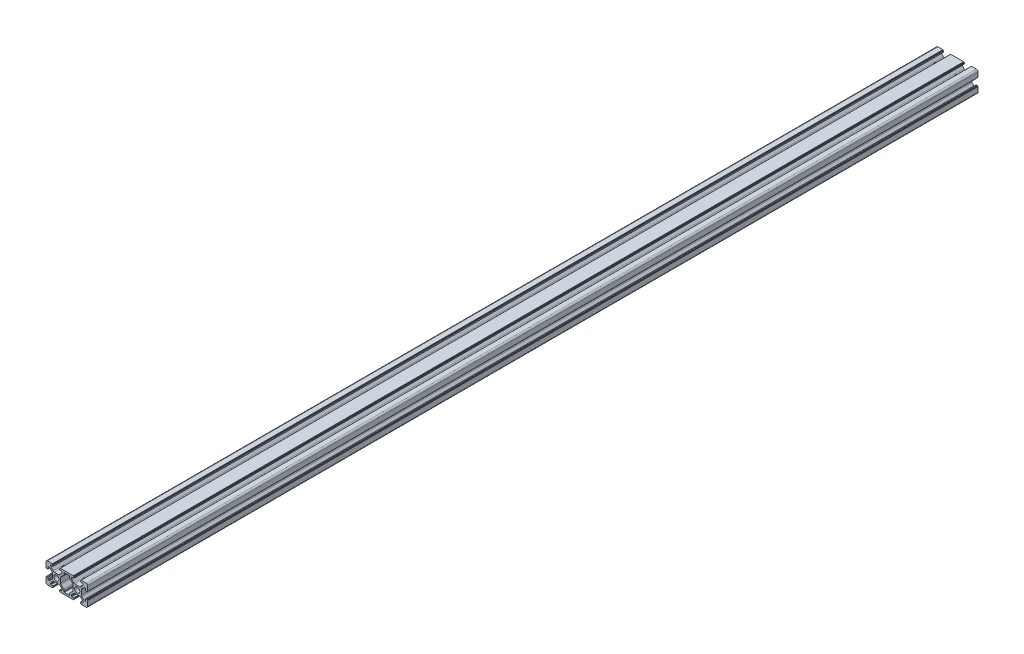
SolidWorks part; units mm, degrees
material "6063-O"
ref_plane "Front Plane" through (0, 0, 0) normal (0, 0, 1) x (1, 0, 0)
ref_plane "Top Plane" through (0, 0, 0) normal (0, 1, 0) x (1, 0, 0)
ref_plane "Right Plane" through (0, 0, 0) normal (1, 0, 0) x (0, 0, -1)
sketch "Sketch1" plane through (0, 0, 0) normal (0, 0, 1) x (1, 0, 0)
  line L0 (1.5, 0) -> (6.2, 0)
  line L1 (40, 1.5) -> (40, 6.2)
  line L2 (38.5, 20) -> (33.8, 20)
  line L3 (0, 18.5) -> (0, 13.8)
  line L4 (17.6, 1.8) -> (22.4, 1.8)
  line L5 (32.218, 13.9) -> (27.782, 13.9)
  line L6 (26.1, 12.218) -> (26.1, 7.782)
  line L7 (17.6, 18.2) -> (22.4, 18.2)
  line L8 (12.218, 13.9) -> (7.9864, 13.9)
  line L9 (6.1, 12.218) -> (6.1, 7.782)
  line L10 (7.782, 6.1) -> (12.218, 6.1)
  line L11 (13.9, 7.782) -> (13.9, 12.218)
  line L12 (27.782, 6.1) -> (32.218, 6.1)
  line L13 (33.9, 7.782) -> (33.9, 12.218)
  line L14 (26.7213, 14.3393) -> (24.9393, 16.1213)
  line L15 (33.2787, 14.3393) -> (35.0607, 16.1213)
  line L16 (34.3393, 13.2787) -> (36.1213, 15.0607)
  line L17 (25.6607, 6.7213) -> (23.1393, 4.2)
  line L18 (15.2, 1.8) -> (13.4, 1.8)
  line L19 (26.7213, 5.6607) -> (24.9393, 3.8787)
  line L20 (24.8, 1.8) -> (26.6, 1.8)
  line L21 (15.3, 18.2) -> (13.1, 18.2)
  line L22 (13.2787, 14.3393) -> (15.1607, 16.2213)
  line L23 (14.3393, 13.2787) -> (16.8607, 15.8)
  line L24 (5.6607, 6.7213) -> (3.8787, 4.9393)
  line L25 (6.7213, 5.6607) -> (4.9393, 3.8787)
  line L26 (6.897, 14.3689) -> (4.9106, 16.4674)
  line L27 (5.6607, 13.2787) -> (3.8787, 15.0607)
  line L28 (14.3393, 6.7213) -> (16.8607, 4.2)
  line L29 (13.2787, 5.6607) -> (15.0607, 3.8787)
  line L30 (24.8, 18.2) -> (26.6, 18.2)
  line L31 (25.6607, 13.2787) -> (23.1393, 15.8)
  line L32 (34.3393, 6.7213) -> (36.1213, 4.9393)
  line L33 (33.2787, 5.6607) -> (35.0607, 3.8787)
  line L34 (1.8, 15.2) -> (1.8, 13.4)
  line L35 (24.5, 2.1) -> (24.5, 2.818)
  line L36 (4.5, 2.1) -> (4.5, 2.818)
  line L37 (2.818, 4.5) -> (2.1, 4.5)
  line L38 (4.5, 17.9) -> (4.5, 17.4986)
  line L39 (2.818, 15.5) -> (2.1, 15.5)
  line L40 (15.6, 17.9) -> (15.6, 17.282)
  line L41 (15.5, 2.818) -> (15.5, 2.1)
  line L42 (38.2, 15.2) -> (38.2, 13.4)
  line L43 (35.5, 2.818) -> (35.5, 2.1)
  line L44 (37.182, 4.5) -> (37.9, 4.5)
  line L45 (35.5, 17.182) -> (35.5, 17.9)
  line L46 (37.182, 15.5) -> (37.9, 15.5)
  line L47 (17.3, 2.1) -> (17.3, 3.1393)
  line L48 (22.7, 2.1) -> (22.7, 3.1393)
  line L49 (17.3, 17.9) -> (17.3, 16.8607)
  line L50 (22.7, 17.9) -> (22.7, 16.8607)
  line L51 (24.5, 17.9) -> (24.5, 17.182)
  line L52 (6.9, 19.3) -> (6.9, 18.2)
  line L53 (13.1, 19.3) -> (13.1, 18.2)
  line L54 (6.9, 1.5) -> (6.9, 0.7)
  line L55 (13.1, 1.5) -> (13.1, 0.7)
  line L56 (13.8, 0) -> (26.2, 0)
  line L57 (6.6, 1.8) -> (4.8, 1.8)
  line L58 (6.9, 18.2) -> (4.8, 18.2)
  line L59 (6.2, 20) -> (1.5, 20)
  line L60 (39.3, 6.9) -> (38.5, 6.9)
  line L61 (39.3, 13.1) -> (38.5, 13.1)
  line L62 (1.5, 13.1) -> (0.7, 13.1)
  line L63 (1.5, 6.9) -> (0.7, 6.9)
  line L64 (0, 6.2) -> (0, 1.5)
  line L65 (1.8, 6.6) -> (1.8, 4.8)
  line L66 (38.2, 6.6) -> (38.2, 4.8)
  line L67 (40, 13.8) -> (40, 18.5)
  line L68 (33.1, 19.3) -> (33.1, 18.5)
  line L69 (26.9, 19.3) -> (26.9, 18.5)
  line L70 (26.9, 1.5) -> (26.9, 0.7)
  line L71 (33.1, 1.5) -> (33.1, 0.7)
  line L72 (33.8, 0) -> (38.5, 0)
  line L73 (33.4, 1.8) -> (35.2, 1.8)
  line L74 (26.2, 20) -> (13.8, 20)
  line L75 (33.4, 18.2) -> (35.2, 18.2)
  line L76 (6.7, 0.5) -> (6.6, 0.5)
  line L77 (6.4, 0.3) -> (6.4, 0.2)
  line L78 (13.3, 0.5) -> (13.4, 0.5)
  line L79 (13.6, 0.3) -> (13.6, 0.2)
  line L80 (26.7, 0.5) -> (26.6, 0.5)
  line L81 (26.4, 0.3) -> (26.4, 0.2)
  line L82 (33.3, 0.5) -> (33.4, 0.5)
  line L83 (33.6, 0.3) -> (33.6, 0.2)
  line L85 (6.4, 19.8) -> (6.4, 19.7)
  line L86 (6.6, 19.5) -> (6.7, 19.5)
  line L87 (13.6, 19.8) -> (13.6, 19.7)
  line L88 (13.4, 19.5) -> (13.3, 19.5)
  line L89 (26.4, 19.8) -> (26.4, 19.7)
  line L90 (26.6, 19.5) -> (26.7, 19.5)
  line L91 (33.6, 19.8) -> (33.6, 19.7)
  line L92 (33.4, 19.5) -> (33.3, 19.5)
  line L93 (0.5, 13.3) -> (0.5, 13.4)
  line L94 (0.3, 13.6) -> (0.2, 13.6)
  line L95 (0.5, 6.7) -> (0.5, 6.6)
  line L96 (0.3, 6.4) -> (0.2, 6.4)
  line L97 (39.5, 13.3) -> (39.5, 13.4)
  line L98 (39.7, 13.6) -> (39.8, 13.6)
  line L99 (39.5, 6.7) -> (39.5, 6.6)
  line L100 (39.7, 6.4) -> (39.8, 6.4)
  circle A0 centre (10, 10) radius 2.5
  circle A1 centre (30, 10) radius 2.5
  arc A2 (38.5, 0) -> (40, 1.5) centre (38.5, 1.5) ccw
  arc A3 (40, 18.5) -> (38.5, 20) centre (38.5, 18.5) ccw
  arc A4 (1.5, 0) -> (0, 1.5) centre (1.5, 1.5) cw
  arc A5 (1.5, 20) -> (0, 18.5) centre (1.5, 18.5) ccw
  arc A6 (26.7213, 5.6607) -> (27.782, 6.1) centre (27.782, 4.6) cw
  arc A7 (32.218, 6.1) -> (33.2787, 5.6607) centre (32.218, 4.6) cw
  arc A8 (33.9, 7.782) -> (34.3393, 6.7213) centre (35.4, 7.782) ccw
  arc A9 (33.2787, 14.3393) -> (32.218, 13.9) centre (32.218, 15.4) cw
  arc A10 (14.3393, 6.7213) -> (13.9, 7.782) centre (15.4, 7.782) cw
  arc A11 (14.3393, 13.2787) -> (13.9, 12.218) centre (15.4, 12.218) ccw
  arc A12 (25.6607, 6.7213) -> (26.1, 7.782) centre (24.6, 7.782) ccw
  arc A13 (26.1, 12.218) -> (25.6607, 13.2787) centre (24.6, 12.218) ccw
  arc A14 (27.782, 13.9) -> (26.7213, 14.3393) centre (27.782, 15.4) cw
  arc A15 (5.6607, 13.2787) -> (6.1, 12.218) centre (4.6, 12.218) cw
  arc A16 (5.6607, 6.7213) -> (6.1, 7.782) centre (4.6, 7.782) ccw
  arc A17 (13.2787, 5.6607) -> (12.218, 6.1) centre (12.218, 4.6) ccw
  arc A18 (6.7213, 5.6607) -> (7.782, 6.1) centre (7.782, 4.6) cw
  arc A19 (13.2787, 14.3393) -> (12.218, 13.9) centre (12.218, 15.4) cw
  arc A20 (6.897, 14.3689) -> (7.9864, 13.9) centre (7.9864, 15.4) ccw
  arc A21 (36.1213, 4.9393) -> (37.182, 4.5) centre (37.182, 6) ccw
  arc A22 (36.1213, 15.0607) -> (37.182, 15.5) centre (37.182, 14) cw
  arc A23 (35.0607, 16.1213) -> (35.5, 17.182) centre (34, 17.182) ccw
  arc A24 (24.5, 17.182) -> (24.9393, 16.1213) centre (26, 17.182) ccw
  arc A25 (22.7, 16.8607) -> (23.1393, 15.8) centre (24.2, 16.8607) ccw
  arc A26 (17.3, 16.8607) -> (16.8607, 15.8) centre (15.8, 16.8607) cw
  arc A27 (4.9106, 16.4674) -> (4.5, 17.4986) centre (6, 17.4986) cw
  arc A28 (15.6, 17.282) -> (15.1607, 16.2213) centre (14.1, 17.282) cw
  arc A29 (3.8787, 15.0607) -> (2.818, 15.5) centre (2.818, 14) ccw
  arc A30 (3.8787, 4.9393) -> (2.818, 4.5) centre (2.818, 6) cw
  arc A31 (4.9393, 3.8787) -> (4.5, 2.818) centre (6, 2.818) ccw
  arc A32 (35.0607, 3.8787) -> (35.5, 2.818) centre (34, 2.818) cw
  arc A33 (24.9393, 3.8787) -> (24.5, 2.818) centre (26, 2.818) ccw
  arc A34 (22.7, 3.1393) -> (23.1393, 4.2) centre (24.2, 3.1393) cw
  arc A35 (17.3, 3.1393) -> (16.8607, 4.2) centre (15.8, 3.1393) ccw
  arc A36 (15.5, 2.818) -> (15.0607, 3.8787) centre (14, 2.818) ccw
  arc A37 (1.8, 6.6) -> (1.5, 6.9) centre (1.5, 6.6) ccw
  arc A38 (1.8, 13.4) -> (1.5, 13.1) centre (1.5, 13.4) cw
  arc A39 (17.6, 18.2) -> (17.3, 17.9) centre (17.6, 17.9) ccw
  arc A40 (22.4, 1.8) -> (22.7, 2.1) centre (22.4, 2.1) ccw
  arc A41 (17.6, 1.8) -> (17.3, 2.1) centre (17.6, 2.1) cw
  arc A42 (15.2, 1.8) -> (15.5, 2.1) centre (15.2, 2.1) ccw
  arc A43 (6.6, 1.8) -> (6.9, 1.5) centre (6.6, 1.5) cw
  arc A44 (13.4, 1.8) -> (13.1, 1.5) centre (13.4, 1.5) ccw
  arc A45 (24.8, 1.8) -> (24.5, 2.1) centre (24.8, 2.1) cw
  arc A46 (35.2, 1.8) -> (35.5, 2.1) centre (35.2, 2.1) ccw
  arc A47 (26.6, 1.8) -> (26.9, 1.5) centre (26.6, 1.5) cw
  arc A48 (33.4, 1.8) -> (33.1, 1.5) centre (33.4, 1.5) ccw
  arc A49 (26.9, 18.5) -> (26.6, 18.2) centre (26.6, 18.5) cw
  arc A50 (33.1, 18.5) -> (33.4, 18.2) centre (33.4, 18.5) ccw
  arc A51 (37.9, 4.5) -> (38.2, 4.8) centre (37.9, 4.8) ccw
  arc A52 (38.5, 13.1) -> (38.2, 13.4) centre (38.5, 13.4) cw
  arc A53 (38.5, 6.9) -> (38.2, 6.6) centre (38.5, 6.6) ccw
  arc A54 (38.2, 15.2) -> (37.9, 15.5) centre (37.9, 15.2) ccw
  arc A55 (35.2, 18.2) -> (35.5, 17.9) centre (35.2, 17.9) cw
  arc A56 (24.8, 18.2) -> (24.5, 17.9) centre (24.8, 17.9) ccw
  arc A57 (22.4, 18.2) -> (22.7, 17.9) centre (22.4, 17.9) cw
  arc A58 (15.3, 18.2) -> (15.6, 17.9) centre (15.3, 17.9) cw
  arc A59 (4.5, 17.9) -> (4.8, 18.2) centre (4.8, 17.9) cw
  arc A60 (1.8, 15.2) -> (2.1, 15.5) centre (2.1, 15.2) cw
  arc A61 (1.8, 4.8) -> (2.1, 4.5) centre (2.1, 4.8) ccw
  arc A62 (4.5, 2.1) -> (4.8, 1.8) centre (4.8, 2.1) ccw
  arc A63 (34.3393, 13.2787) -> (33.9, 12.218) centre (35.4, 12.218) ccw
  arc A64 (6.4, 0.2) -> (6.2, 0) centre (6.2, 0.2) cw
  arc A65 (6.6, 0.5) -> (6.4, 0.3) centre (6.6, 0.3) ccw
  arc A66 (6.7, 0.5) -> (6.9, 0.7) centre (6.7, 0.7) ccw
  arc A67 (13.6, 0.2) -> (13.8, 0) centre (13.8, 0.2) ccw
  arc A68 (13.4, 0.5) -> (13.6, 0.3) centre (13.4, 0.3) cw
  arc A69 (13.3, 0.5) -> (13.1, 0.7) centre (13.3, 0.7) cw
  arc A70 (26.4, 0.2) -> (26.2, 0) centre (26.2, 0.2) cw
  arc A71 (26.6, 0.5) -> (26.4, 0.3) centre (26.6, 0.3) ccw
  arc A72 (26.7, 0.5) -> (26.9, 0.7) centre (26.7, 0.7) ccw
  arc A73 (33.6, 0.2) -> (33.8, 0) centre (33.8, 0.2) ccw
  arc A74 (33.4, 0.5) -> (33.6, 0.3) centre (33.4, 0.3) cw
  arc A75 (33.3, 0.5) -> (33.1, 0.7) centre (33.3, 0.7) cw
  arc A76 (39.8, 6.4) -> (40, 6.2) centre (39.8, 6.2) cw
  arc A77 (39.5, 6.6) -> (39.7, 6.4) centre (39.7, 6.6) ccw
  arc A78 (39.5, 6.7) -> (39.3, 6.9) centre (39.3, 6.7) ccw
  arc A79 (39.5, 13.3) -> (39.3, 13.1) centre (39.3, 13.3) cw
  arc A80 (39.5, 13.4) -> (39.7, 13.6) centre (39.7, 13.4) cw
  arc A81 (39.8, 13.6) -> (40, 13.8) centre (39.8, 13.8) ccw
  arc A82 (33.3, 19.5) -> (33.1, 19.3) centre (33.3, 19.3) ccw
  arc A83 (33.6, 19.7) -> (33.4, 19.5) centre (33.4, 19.7) cw
  arc A84 (33.6, 19.8) -> (33.8, 20) centre (33.8, 19.8) cw
  arc A85 (26.7, 19.5) -> (26.9, 19.3) centre (26.7, 19.3) cw
  arc A86 (26.4, 19.7) -> (26.6, 19.5) centre (26.6, 19.7) ccw
  arc A87 (26.4, 19.8) -> (26.2, 20) centre (26.2, 19.8) ccw
  arc A88 (0.2, 6.4) -> (0, 6.2) centre (0.2, 6.2) ccw
  arc A89 (0.5, 6.6) -> (0.3, 6.4) centre (0.3, 6.6) cw
  arc A90 (0.5, 6.7) -> (0.7, 6.9) centre (0.7, 6.7) cw
  arc A91 (13.3, 19.5) -> (13.1, 19.3) centre (13.3, 19.3) ccw
  arc A92 (13.6, 19.7) -> (13.4, 19.5) centre (13.4, 19.7) cw
  arc A93 (13.6, 19.8) -> (13.8, 20) centre (13.8, 19.8) cw
  arc A94 (6.2, 20) -> (6.4, 19.8) centre (6.2, 19.8) cw
  arc A95 (6.7, 19.5) -> (6.9, 19.3) centre (6.7, 19.3) cw
  arc A96 (6.4, 19.7) -> (6.6, 19.5) centre (6.6, 19.7) ccw
  arc A97 (0.5, 13.3) -> (0.7, 13.1) centre (0.7, 13.3) ccw
  arc A98 (0.2, 13.6) -> (0, 13.8) centre (0.2, 13.8) cw
  arc A99 (0.5, 13.4) -> (0.3, 13.6) centre (0.3, 13.4) ccw
  point P87 (0, 0)
  point P178 (1.8, 6.9)
  point P181 (1.8, 13.1)
  point P186 (22.7, 1.8)
  point P193 (6.9, 1.8)
  point P204 (33.1, 1.8)
  point P209 (33.1, 18.2)
  point P216 (38.2, 6.9)
  point P243 (6.9, 0.5)
  point P248 (13.6, 0.5)
  point P257 (26.9, 0.5)
extrude "Boss-Extrude2" add sketch "Sketch1" along normal blind 856 contours A57 L7 A39 L49 A26 L23 A11 L11 A10 L28 A35 L47 A41 L4 A40 L48 A34 L17 A12 L6 A13 L31 A25 L50 | A0 | A1 | L59 A5 L3 A98 L94 A99 L93 A97 L62 A38 L34 A60 L39 A29 L27 A15 L9 A16 L24 A30 L37 A61 L65 A37 L63 A90 L95 A89 L96 A88 L64 A4 L0 A64 L77 A65 L76 A66 L54 A43 L57 A62 L36 A31 L25 A18 L10 A17 L29 A36 L41 A42 L18 A44 L55 A69 L78 A68 L79 A67 L56 A70 L81 A71 L80 A72 L70 A47 L20 A45 L35 A33 L19 A6 L12 A7 L33 A32 L43 A46 L73 A48 L71 A75 L82 A74 L83 A73 L72 A2 L1 A76 L100 A77 L99 A78 L60 A53 L66 A51 L44 A21 L32 A8 L13 A63 L16 A22 L46 A54 L42 A52 L61 A79 L97 A80 L98 A81 L67 A3 L2 A84 L91 A83 L92 A82 L68 A50 L75 A55 L45 A23 L15 A9 L5 A14 L14 A24 L51 A56 L30 A49 L69 A85 L90 A86 L89 A87 L74 A93 L87 A92 L88 A91 L53 L21 A58 L40 A28 L22 A19 L8 A20 L26 A27 L38 A59 L58 L52 A95 L86 A96 L85 A94
hole_wizard "M5 Clearance Hole1" positions "Sketch2" profile "Sketch3" hole size "M5" standard "ISO"
sketch "Sketch2" plane through (0, 6.1, 0) normal (0, -1, 0) x (-1, 0, 0)
  point P0 (-30, -847)
  point P3 (-10, -847)
  point P7 (-30, -9)
  point P10 (-10, -9)
sketch "Sketch3" plane through (30, 6.1, 847) normal (1, 0, 0) x (0, 0, -1)
  line L0 (0, 0) -> (0, 13.9)
  line L1 (0, 13.9) -> (2.75, 13.9)
  line L2 (2.75, 13.9) -> (2.75, 0)
  line L5 (2.75, 0) -> (0, 0)
  line L11 (0, -6.35) -> (0, 107.95) construction
  dimension "Thru Hole Dia." = 5.5
  dimension "Thru Hole Depth" = 13.9
